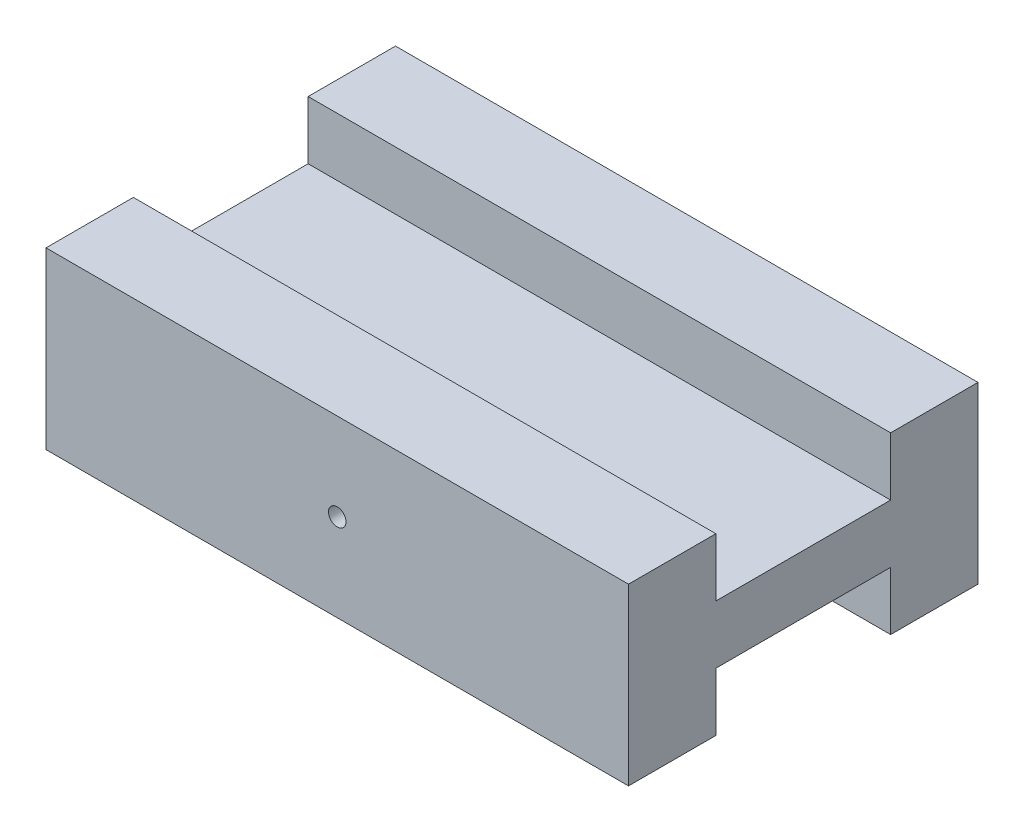
SolidWorks part; units mm, degrees
ref_plane "Front Plane" through (0, 0, 0) normal (0, 0, 1) x (1, 0, 0)
ref_plane "Top Plane" through (0, 0, 0) normal (0, 1, 0) x (1, 0, 0)
ref_plane "Right Plane" through (0, 0, 0) normal (1, 0, 0) x (0, 0, -1)
sketch "Sketch1" plane through (0, 0, 0) normal (0, 1, 0) x (1, 0, 0)
  line L1 (0, 0) -> (50, 0)
  line L2 (0, 0) -> (0, 30)
  line L3 (0, 30) -> (50, 30)
  line L4 (50, 0) -> (50, 30)
  dimension "D1" = 50
  dimension "D2" = 30
extrude "Boss-Extrude1" add sketch "Sketch1" along normal blind 15
sketch "Sketch2" plane through (0, 15, 0) normal (0, 1, 0) x (1, 0, 0)
  line L0 (0, 30) -> (0, 0) construction
  line L1 (0, 22.5) -> (50, 22.5)
  line L2 (0, 22.5) -> (0, 7.5)
  line L3 (0, 7.5) -> (50, 7.5)
  line L4 (50, 22.5) -> (50, 7.5)
  line L5 (50, 0) -> (50, 30) construction
  line L6 (50, 30) -> (0, 30) construction
  dimension "D1" = 15
  dimension "D2" = 7.5
extrude "Cut-Extrude1" cut sketch "Sketch2" against normal blind 5
sketch "Sketch3" plane through (0, 0, 0) normal (0, -1, 0) x (1, 0, 0)
  line L0 (50, 0) -> (50, -30) construction
  line L1 (0, -30) -> (0, 0) construction
  line L2 (50, -22.5) -> (0, -22.5) construction
  line L3 (0, -7.5) -> (50, -7.5) construction
  line L4 (50, -7.5) -> (50, -22.5)
  line L5 (0, -22.5) -> (0, -7.5)
  line L6 (50, -22.5) -> (0, -22.5)
  line L7 (0, -7.5) -> (50, -7.5)
extrude "Cut-Extrude2" cut sketch "Sketch3" against normal blind 5
sketch "Sketch4" plane through (0, 0, 0) normal (0, 0, 1) x (1, 0, 0)
  line L0 (0, 7.5) -> (50, 7.5) construction
  line L1 (0, 15) -> (0, 0) construction
  line L2 (50, 15) -> (50, 0) construction
  circle A0 centre (25, 7.5) radius 0.75
  dimension "D1" = 1.5
extrude "Cut-Extrude3" cut sketch "Sketch4" against normal up to surface (30 mm away) up to face at (25, 7.5, -30)
